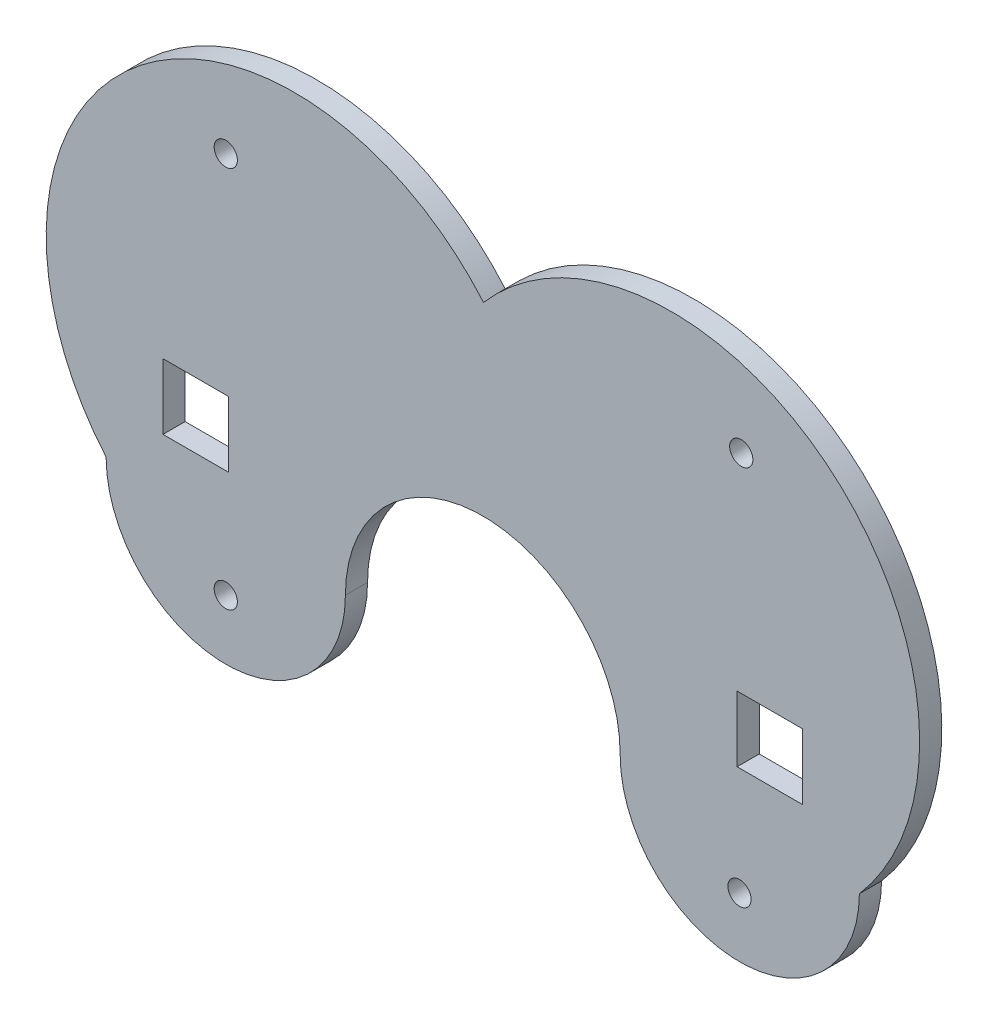
SolidWorks part; units mm, degrees
ref_plane "Front Plane" through (0, 0, 0) normal (0, 0, 1) x (1, 0, 0)
ref_plane "Top Plane" through (0, 0, 0) normal (0, 1, 0) x (1, 0, 0)
ref_plane "Right Plane" through (0, 0, 0) normal (1, 0, 0) x (0, 0, -1)
sketch "Sketch1" plane through (0, 0, 0) normal (0, 0, 1) x (1, 0, 0)
  arc A1 (34.2886, 17.145) -> (-0.0014, 17.145) centre (17.1436, 17.145) cw
  arc A2 (-0.0014, 17.145) -> (54.081, 63.3761) centre (26.9868, 40.3225) cw
  arc A4 (34.2886, 17.145) -> (73.6613, 17.0875) centre (53.975, 17.145) cw
  arc A5 (73.6613, 17.0875) -> (107.9502, 16.9297) centre (90.8059, 17.0374) ccw
  arc A9 (54.081, 63.3761) -> (107.9502, 16.9297) centre (81.0156, 40.1529) cw
extrude "Boss-Extrude1" add sketch "Sketch1" along normal blind 3.175 contours A9 A5 A4 A1 A2
sketch "Sketch2" plane through (0, 0, 3.175) normal (0, 0, 1) x (1, 0, 0)
  line L0 (-0.0014, 17.145) -> (34.2886, 17.145) construction
  line L1 (34.2886, 17.145) -> (17.1436, 0) construction
  line L2 (17.1436, 0) -> (-0.0014, 17.145) construction
  line L3 (73.6612, 17.0374) -> (107.9502, 16.9297) construction
  line L4 (107.9502, 16.9297) -> (90.727, -0.1071) construction
  line L5 (90.727, -0.1071) -> (73.6612, 17.0374) construction
  line L6 (17.1436, 17.145) -> (17.1436, 0) construction
  line L7 (90.727, -0.1071) -> (90.8057, 16.9836) construction
  line L8 (17.1436, 8.5725) -> (17.1436, 74.5083) construction
  line L9 (54.081, 63.3761) -> (54.0038, 36.8313) construction
  line L10 (90.6989, 8.3586) -> (91.0824, 74.2933) construction
  line L11 (-8.5879, 40.3225) -> (116.5794, 40.1529) construction
  arc A0 (-0.0014, 17.145) -> (34.2886, 17.145) centre (17.1436, 17.145) ccw construction
  arc A1 (73.6613, 17.0875) -> (107.9502, 16.9297) centre (90.8059, 17.0374) ccw construction
  circle A2 centre (17.1436, 8.5725) radius 1.6637
  circle A3 centre (90.7663, 8.4382) radius 1.6637
  arc A4 (54.081, 63.3761) -> (-0.0014, 17.145) centre (26.9868, 40.3225) ccw construction
  arc A5 (73.6613, 17.0875) -> (34.2886, 17.145) centre (53.975, 17.145) ccw construction
  arc A6 (107.9502, 16.9297) -> (54.081, 63.3761) centre (81.0156, 40.1529) ccw construction
  circle A7 centre (17.1436, 63.3761) radius 1.6637
  circle A8 centre (91.0176, 63.1612) radius 1.6637
  point P42 (0, 0)
  dimension "D1" = 3.3274
  dimension "D2" = 3.3274
  dimension "D3" = 3.3274
extrude "Cut-Extrude1" cut sketch "Sketch2" against normal blind 3.175
sketch "Sketch3" plane through (0, 0, 3.175) normal (0, 0, 1) x (1, 0, 0)
  line L0 (-8.5879, 40.3225) -> (34.2886, 17.145) construction
  line L1 (116.5794, 40.1529) -> (73.6613, 17.0875) construction
  line L3 (8.1514, 24.0347) -> (17.5494, 24.0347)
  line L4 (8.1514, 24.0347) -> (8.1514, 33.4327)
  line L5 (8.1514, 33.4327) -> (17.5494, 33.4327)
  line L6 (17.5494, 24.0347) -> (17.5494, 33.4327)
  line L7 (8.1514, 24.0347) -> (17.5494, 33.4327) construction
  line L8 (8.1514, 33.4327) -> (17.5494, 24.0347) construction
  line L9 (90.4213, 23.9212) -> (99.8193, 23.9212)
  line L10 (90.4213, 23.9212) -> (90.4213, 33.3192)
  line L11 (90.4213, 33.3192) -> (99.8193, 33.3192)
  line L12 (99.8193, 23.9212) -> (99.8193, 33.3192)
  line L13 (90.4213, 23.9212) -> (99.8193, 33.3192) construction
  line L14 (90.4213, 33.3192) -> (99.8193, 23.9212) construction
  arc A0 (54.081, 63.3761) -> (-0.0014, 17.145) centre (26.9868, 40.3225) ccw construction
  arc A1 (107.9502, 16.9297) -> (54.081, 63.3761) centre (81.0156, 40.1529) ccw construction
  point P12 (12.8504, 28.7337)
  point P17 (95.1203, 28.6202)
  dimension "D1" = 9.398
  dimension "D2" = 9.398
  dimension "D3" = 9.398
  dimension "D4" = 9.398
extrude "Cut-Extrude2" cut sketch "Sketch3" against normal blind 3.175
